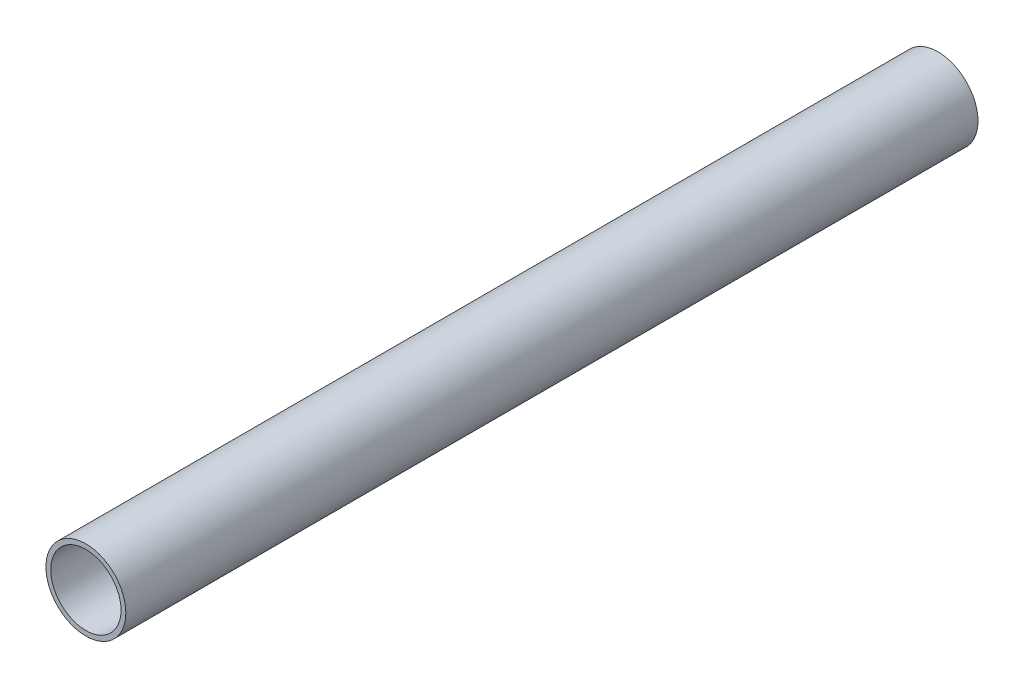
SolidWorks part; units mm, degrees
ref_plane "Front Plane" through (0, 0, 0) normal (0, 0, 1) x (1, 0, 0)
ref_plane "Top Plane" through (0, 0, 0) normal (0, 1, 0) x (1, 0, 0)
ref_plane "Right Plane" through (0, 0, 0) normal (1, 0, 0) x (0, 0, -1)
sketch "Sketch1" plane through (0, 0, 0) normal (0, 0, 1) x (1, 0, 0)
  circle A0 centre (0, 0) radius 9.525
  circle A1 centre (0, 0) radius 8.382
  dimension "D1" = 1.143
extrude "Boss-Extrude1" add sketch "Sketch1" along normal blind 203.2
